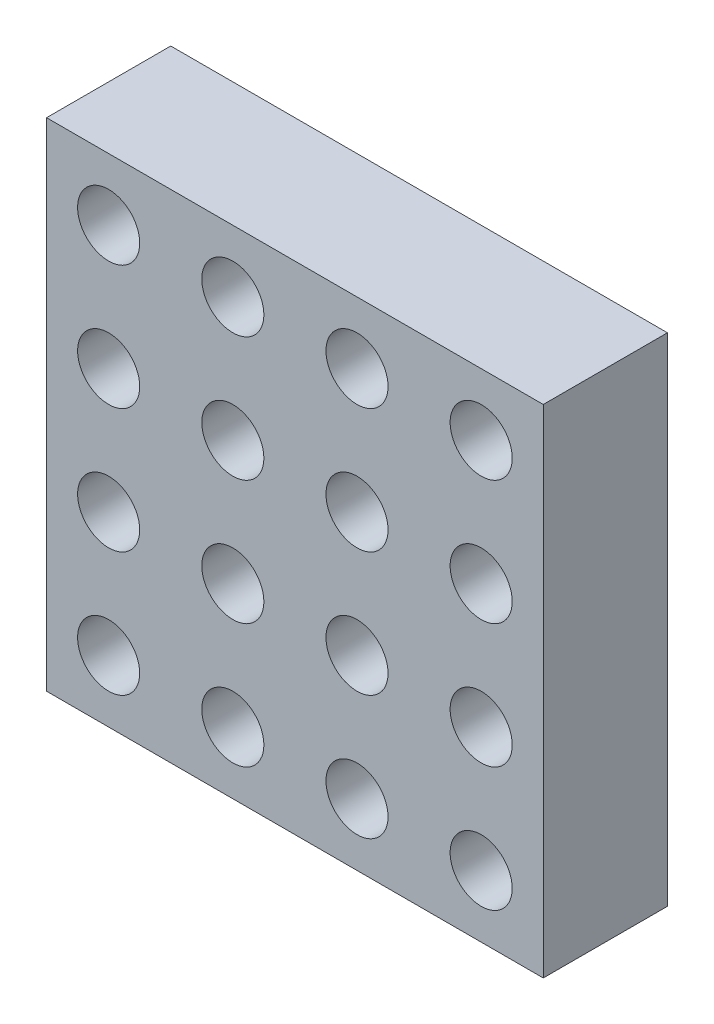
SolidWorks part; units mm, degrees
ref_plane "Front Plane" through (0, 0, 0) normal (0, 0, 1) x (1, 0, 0)
ref_plane "Top Plane" through (0, 0, 0) normal (0, 1, 0) x (1, 0, 0)
ref_plane "Right Plane" through (0, 0, 0) normal (1, 0, 0) x (0, 0, -1)
sketch "Sketch1" plane through (0, 0, 0) normal (0, 0, 1) x (1, 0, 0)
  line L1 (-20, 20) -> (20, 20)
  line L2 (-20, 20) -> (-20, -20)
  line L3 (-20, -20) -> (20, -20)
  line L4 (20, 20) -> (20, -20)
  line L5 (-20, 20) -> (20, -20) construction
  line L6 (-20, -20) -> (20, 20) construction
  point P0 (0, 0)
  dimension "D1" = 40
  dimension "D2" = 40
extrude "Boss-Extrude1" add sketch "Sketch1" along normal blind 10
sketch "Sketch3" plane through (0, 0, 10) normal (0, 0, 1) x (1, 0, 0)
  line L0 (0, 21.4294) -> (0, -22.8822) construction
  line L1 (-25.4247, 0) -> (27.4425, 0) construction
  circle A0 centre (15, 15) radius 2.5
  dimension "D1" = 5
  dimension "D2" = 15
  dimension "D3" = 15
extrude "Cut-Extrude1" cut sketch "Sketch3" against normal through all
pattern_linear "LPattern1" count 4 spacing 10 along (-1, 0, 0) count 4 spacing 10 along (0, -1, 0) of "Cut-Extrude1"
